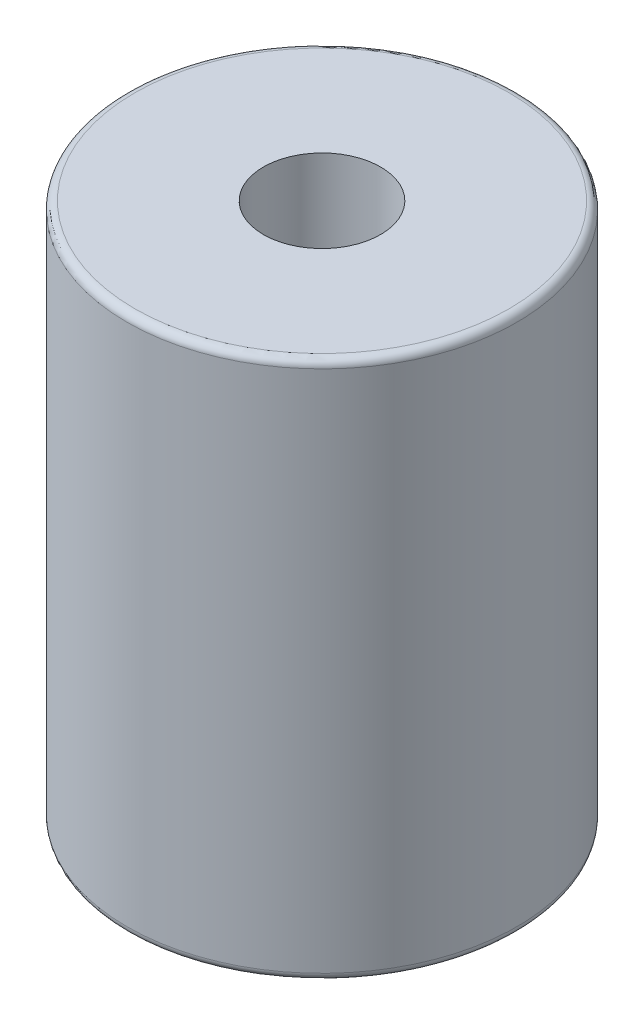
SolidWorks part; units mm, degrees
ref_plane "Alzado" through (0, 0, 0) normal (0, 0, 1) x (1, 0, 0)
ref_plane "Planta" through (0, 0, 0) normal (0, 1, 0) x (1, 0, 0)
ref_plane "Vista lateral" through (0, 0, 0) normal (1, 0, 0) x (0, 0, -1)
sketch "Croquis1" plane through (0, 0, 0) normal (0, 1, 0) x (1, 0, 0)
  circle A0 centre (0, 0) radius 2.495
  dimension "D1" = 4.99
extrude "Saliente-Extruir1" add sketch "Croquis1" along normal blind 6.9
fillet "Redondeo1" radius 0.1 2 edges at (0, 0, 2.495) (0, 6.9, 2.495)
sketch "Croquis2" plane through (0, 6.9, 0) normal (0, 1, 0) x (1, 0, 0)
  circle A0 centre (0, 0) radius 0.75
  dimension "D1" = 1.5
extrude "Cortar-Extruir1" cut sketch "Croquis2" against normal blind 3
